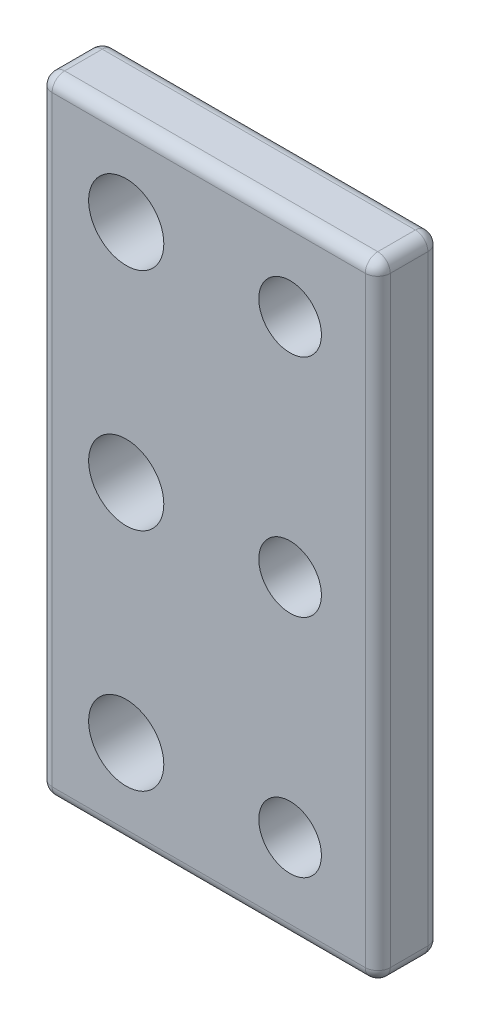
SolidWorks part; units mm, degrees
ref_plane "Płaszczyzna przednia" through (0, 0, 0) normal (0, 0, 1) x (1, 0, 0)
ref_plane "Płaszczyzna górna" through (0, 0, 0) normal (0, 1, 0) x (1, 0, 0)
ref_plane "Płaszczyzna prawa" through (0, 0, 0) normal (1, 0, 0) x (0, 0, -1)
sketch "Sketch1" plane through (0, 0, 0) normal (0, 0, 1) x (1, 0, 0)
  line L0 (-6.583, 25) -> (-6.583, -25) construction
  line L1 (-13.5, 25) -> (13.5, 25)
  line L2 (-13.5, 25) -> (-13.5, -25)
  line L3 (-13.5, -25) -> (13.5, -25)
  line L4 (13.5, 25) -> (13.5, -25)
  line L5 (-13.5, 25) -> (13.5, -25) construction
  line L6 (-13.5, -25) -> (13.5, 25) construction
  line L7 (6.5, 25) -> (6.5, -25) construction
  line L8 (13.5, 18) -> (-13.5, 18) construction
  line L9 (13.5, -18) -> (-13.5, -18) construction
  line L10 (13.5, 0) -> (-13.5, 0) construction
  circle A0 centre (-6.583, 18) radius 3
  circle A1 centre (-6.583, 0) radius 3
  circle A2 centre (-6.583, -18) radius 3
  circle A3 centre (6.5, 18) radius 2.5
  circle A4 centre (6.5, 0) radius 2.5
  circle A5 centre (6.5, -18) radius 2.5
  point P0 (0, 0)
  dimension "D1" = 27
  dimension "D2" = 50
  dimension "D3" = 7
  dimension "D4" = 7
  dimension "D5" = 7
extrude "Boss-Extrude1" add sketch "Sketch1" along normal blind 5
fillet "Fillet2" radius 1 12 edges at (0, -25, 5) (0, -25, 0) (13.5, -25, 2.5) (13.5, 0, 5) (13.5, 0, 0) (13.5, 25, 2.5) (0, 25, 5) (0, 25, 0) (-13.5, 25, 2.5) (-13.5, 0, 5) (-13.5, -25, 2.5) (-13.5, 0, 0)
